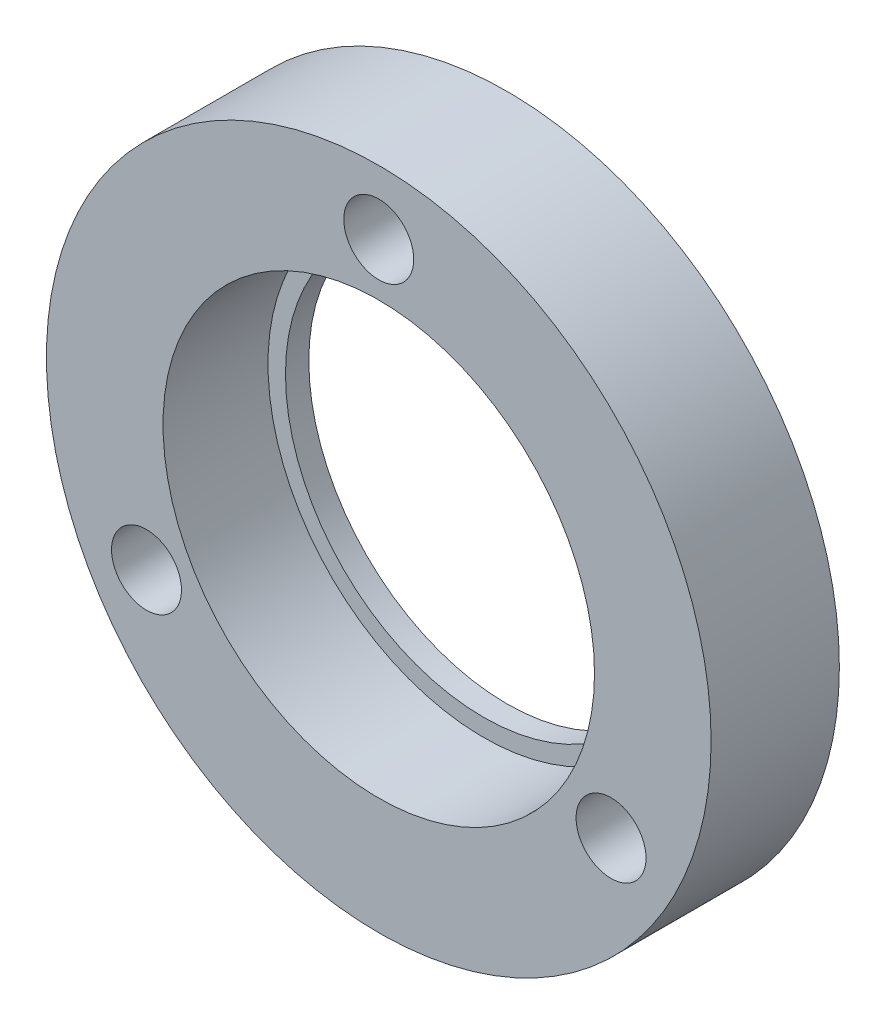
SolidWorks part; units mm, degrees
ref_plane "前视基准面" through (0, 0, 0) normal (0, 0, 1) x (1, 0, 0)
ref_plane "上视基准面" through (0, 0, 0) normal (0, 1, 0) x (1, 0, 0)
ref_plane "右视基准面" through (0, 0, 0) normal (1, 0, 0) x (0, 0, -1)
sketch "草图1" plane through (0, 0, 0) normal (0, 0, 1) x (1, 0, 0)
  circle A0 centre (0, 0) radius 28.5
  dimension "D1" = 57
extrude "凸台-拉伸1" add sketch "草图1" along normal blind 11
sketch "草图3" plane through (0, 0, 11) normal (0, 0, 1) x (1, 0, 0)
  circle A0 centre (0, 0) radius 18.5
extrude "切除-拉伸1" cut sketch "草图3" against normal blind 9
sketch "草图4" plane through (0, 0, 2) normal (0, 0, 1) x (1, 0, 0)
  circle A0 centre (0, 0) radius 17
extrude "切除-拉伸2" cut sketch "草图4" against normal through all
sketch "草图5" plane through (0, 0, 11) normal (0, 0, 1) x (1, 0, 0)
  circle A0 centre (0, 0) radius 23 construction
  circle A1 centre (0, 23) radius 3
  circle A2 centre (19.9186, -11.5) radius 3
  circle A3 centre (-19.9186, -11.5) radius 3
  point P13 (0, 0)
  dimension "D1" = 46
  dimension "D2" = 6
  dimension "D3" = 3
extrude "切除-拉伸3" cut sketch "草图5" against normal through all
